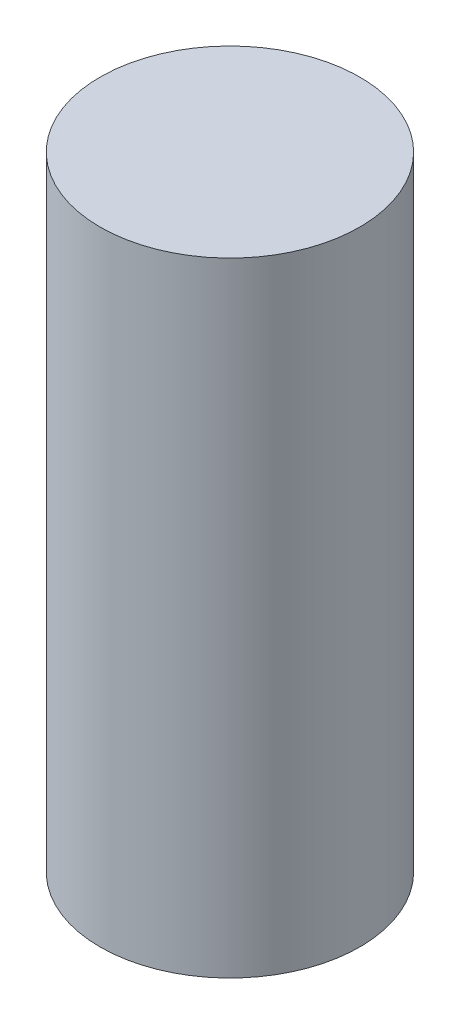
SolidWorks part; units mm, degrees
ref_plane "Front Plane" through (0, 0, 0) normal (0, 0, 1) x (1, 0, 0)
ref_plane "Top Plane" through (0, 0, 0) normal (0, 1, 0) x (1, 0, 0)
ref_plane "Right Plane" through (0, 0, 0) normal (1, 0, 0) x (0, 0, -1)
ref_plane "Plane1" through (0, 0, 0) normal (0, 0, 1) x (1, 0, 0)
sketch "Sketch1" plane through (0, 0, 0) normal (0, 0, 1) x (1, 0, 0)
  line L0 (0, 16.125) -> (1, 16.125)
  line L1 (1, 16.125) -> (1, 11.325)
  line L2 (1, 11.325) -> (0, 11.325)
  line L3 (0, 11.325) -> (0, 16.125)
  line L4 (0, -50) -> (0, 50) construction
revolve "Revolve1" add sketch "Sketch1" angle 360 about L4
